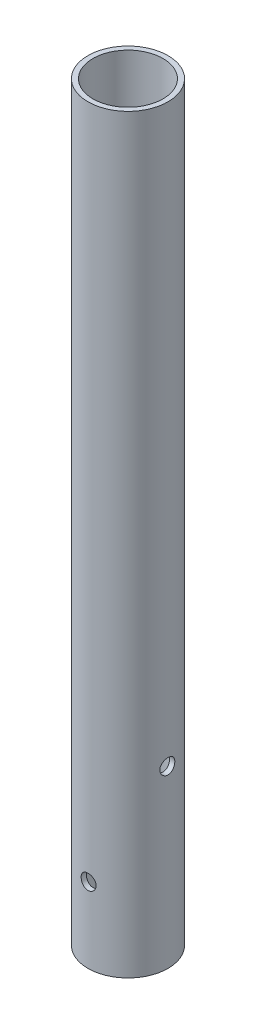
SolidWorks part; units mm, degrees
ref_plane "Front" through (0, 0, 0) normal (0, 0, 1) x (1, 0, 0)
ref_plane "Top" through (0, 0, 0) normal (0, 1, 0) x (1, 0, 0)
ref_plane "Right" through (0, 0, 0) normal (1, 0, 0) x (0, 0, -1)
sketch "草图1" plane through (0, 0, 0) normal (0, 1, 0) x (1, 0, 0)
  circle A0 centre (0, 0) radius 8
  circle A1 centre (0, 0) radius 7
  dimension "D1" = 16
  dimension "D2" = 14
extrude "凸台-拉伸1" add sketch "草图1" along normal blind 150
sketch "草图2" plane through (0, 0, 0) normal (0, 0, 1) x (1, 0, 0)
  line L0 (0, 0) -> (0, 68.563) construction
  line L1 (-8, 0) -> (8, 0) construction
  circle A0 centre (0, 15) radius 1.5
  dimension "D1" = 3
  dimension "D2" = 15
extrude "切除-拉伸1" cut sketch "草图2" against normal through all both and the other way through all
sketch "草图4" plane through (0, 0, 0) normal (1, 0, 0) x (0, 0, -1)
  line L0 (0, 0) -> (0, 96.9677) construction
  line L1 (-8, 0) -> (8, 0) construction
  circle A0 centre (0, 35) radius 1.5
  dimension "D1" = 3
  dimension "D2" = 35
extrude "切除-拉伸2" cut sketch "草图4" against normal through all both and the other way through all
